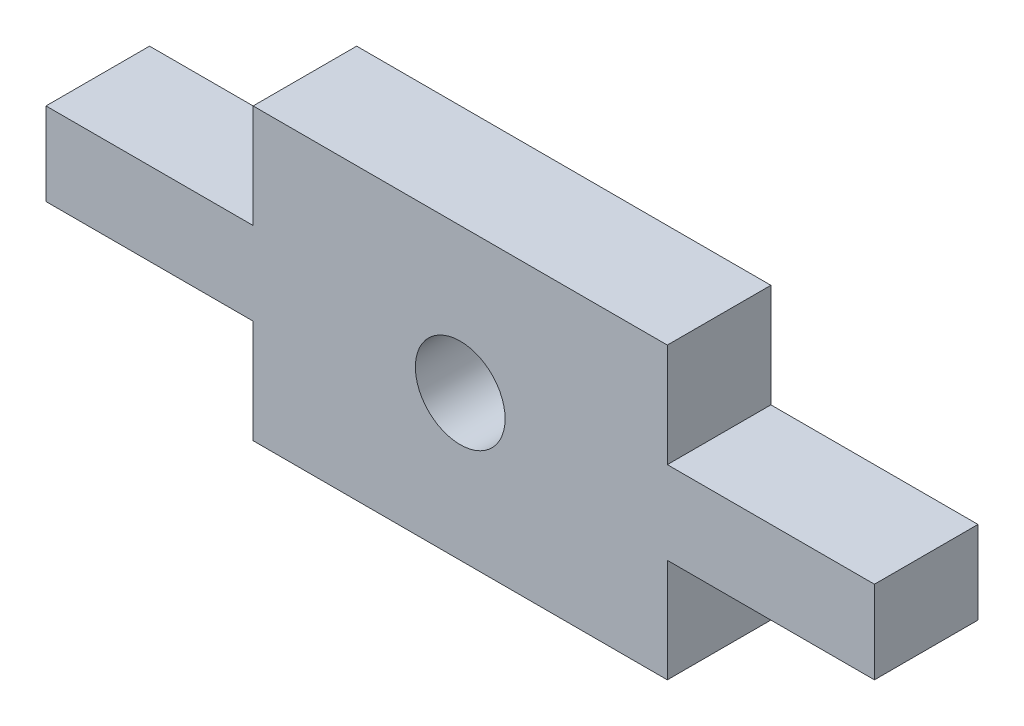
SolidWorks part; units mm, degrees
ref_plane "Front Plane" through (0, 0, 0) normal (0, 0, 1) x (1, 0, 0)
ref_plane "Top Plane" through (0, 0, 0) normal (0, 1, 0) x (1, 0, 0)
ref_plane "Right Plane" through (0, 0, 0) normal (1, 0, 0) x (0, 0, -1)
sketch "Model" plane through (0, 0, 0) normal (0, 0, 1) x (1, 0, 0)
  line L0 (48, 38.2001) -> (54, 38.2)
  line L1 (48, 35.8) -> (54, 35.8001)
  line L2 (66, 35.8001) -> (72, 35.8)
  line L3 (66.0001, 38.1999) -> (72, 38.2001)
  line L4 (66, 41.2) -> (54.0001, 41.2)
  line L5 (54.0001, 41.2) -> (54, 38.2)
  line L6 (48, 38.2001) -> (48, 35.8)
  line L7 (54, 35.8001) -> (54.0001, 32.8)
  line L8 (66, 35.8001) -> (66, 32.8)
  line L9 (66.0001, 38.1999) -> (66, 41.2)
  line L10 (72, 38.2001) -> (72, 35.8)
  line L11 (66, 32.8) -> (54.0001, 32.8)
  circle A0 centre (60.0001, 37) radius 1.3
extrude "Boss-Extrude1" add sketch "Model" along normal blind 3
